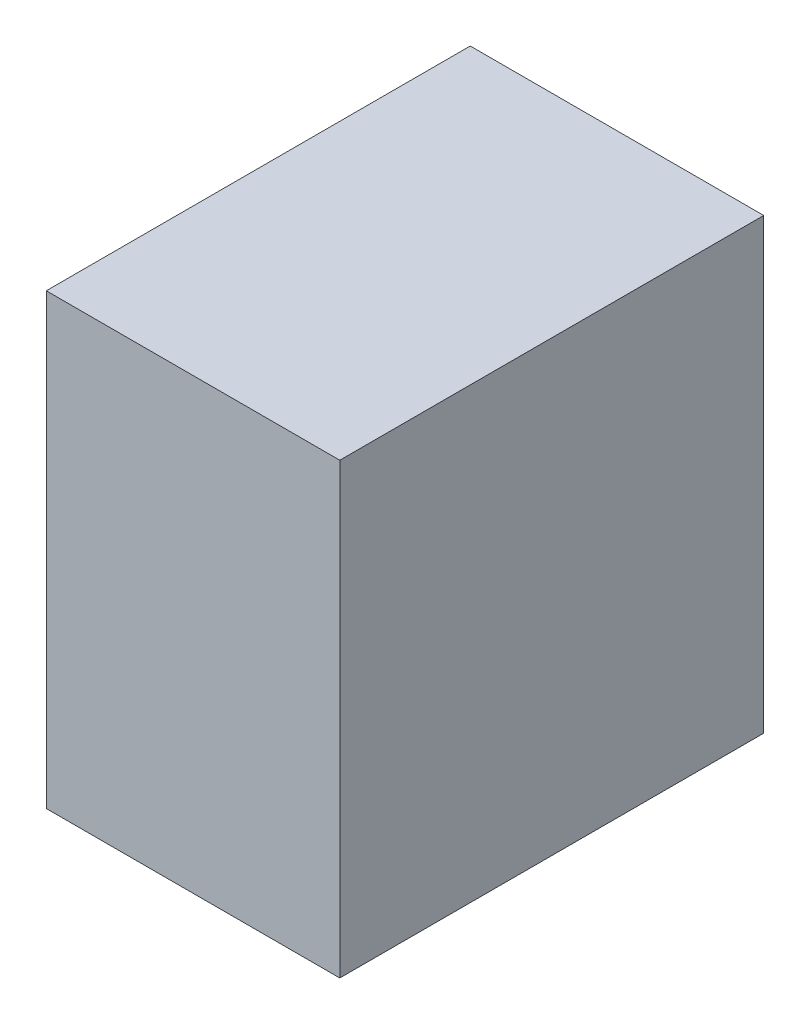
SolidWorks part; units mm, degrees
ref_plane "Plan de face" through (0, 0, 0) normal (0, 0, 1) x (1, 0, 0)
ref_plane "Plan de dessus" through (0, 0, 0) normal (0, 1, 0) x (1, 0, 0)
ref_plane "Plan de droite" through (0, 0, 0) normal (1, 0, 0) x (0, 0, -1)
sketch "Esquisse1" plane through (0, 0, 0) normal (0, 1, 0) x (1, 0, 0)
  line L1 (-85.4848, 24.1006) -> (-49.4848, 24.1006)
  line L2 (-85.4848, 24.1006) -> (-85.4848, -27.8994)
  line L3 (-85.4848, -27.8994) -> (-49.4848, -27.8994)
  line L4 (-49.4848, 24.1006) -> (-49.4848, -27.8994)
  dimension "D1" = 52
  dimension "D2" = 36
extrude "Boss.-Extru.1" add sketch "Esquisse1" along normal blind 55
